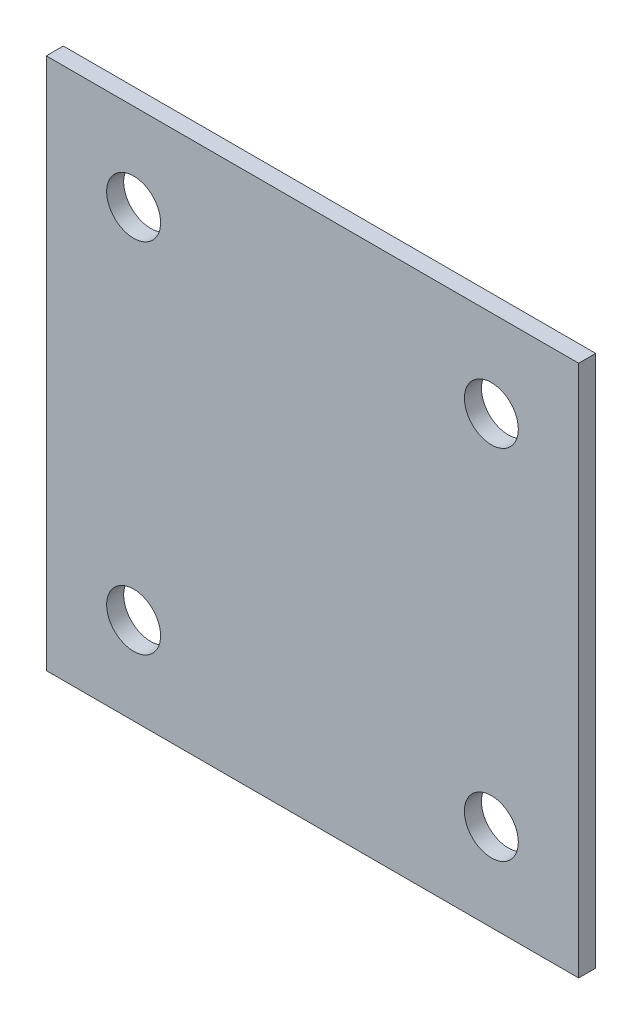
SolidWorks part; units mm, degrees
ref_plane "Front" through (0, 0, 0) normal (0, 0, 1) x (1, 0, 0)
ref_plane "Top" through (0, 0, 0) normal (0, 1, 0) x (1, 0, 0)
ref_plane "Right" through (0, 0, 0) normal (1, 0, 0) x (0, 0, -1)
sketch "Sketch1" plane through (0, 0, 0) normal (0, 0, 1) x (1, 0, 0)
  line L0 (-23.8125, 23.8125) -> (23.8125, -23.8125) construction
  line L1 (-23.8125, 23.8125) -> (23.8125, 23.8125)
  line L2 (-23.8125, 23.8125) -> (-23.8125, -23.8125)
  line L3 (-23.8125, -23.8125) -> (23.8125, -23.8125)
  line L4 (23.8125, 23.8125) -> (23.8125, -23.8125)
  line L5 (-16, -16) -> (16, 16) construction
  line L6 (-16, 16) -> (16, 16) construction
  line L7 (-16, 16) -> (-16, -16) construction
  line L8 (-16, -16) -> (16, -16) construction
  line L9 (16, 16) -> (16, -16) construction
  circle A0 centre (-16, 16) radius 2.413
  circle A1 centre (16, 16) radius 2.413
  circle A2 centre (-16, -16) radius 2.413
  circle A3 centre (16, -16) radius 2.413
  dimension "Hole Size" = 4.826
  dimension "A1" = 47.625
  dimension "B" = 47.625
  dimension "Hole Spacing" = 32
extrude "Boss-Extrude1" add sketch "Sketch1" against normal blind 1.524
